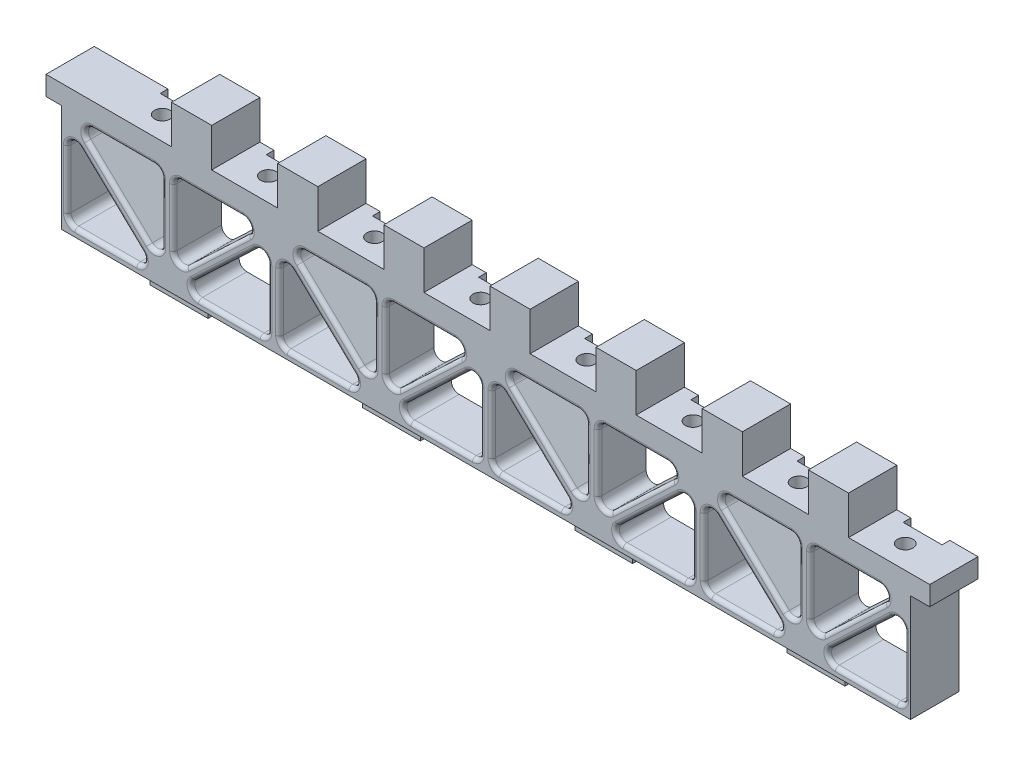
SolidWorks part; units mm, degrees
ref_plane "Front Plane" through (0, 0, 0) normal (0, 0, 1) x (1, 0, 0)
ref_plane "Top Plane" through (0, 0, 0) normal (0, 1, 0) x (1, 0, 0)
ref_plane "Right Plane" through (0, 0, 0) normal (1, 0, 0) x (0, 0, -1)
sketch "Sketch1" plane through (0, 0, 0) normal (0, 1, 0) x (1, 0, 0)
  line L1 (0, 0) -> (228.98, 0)
  line L2 (0, 0) -> (0, 12.5)
  line L3 (0, 12.5) -> (228.98, 12.5)
  line L4 (228.98, 0) -> (228.98, 12.5)
  dimension "D1" = 12.5
  dimension "D2" = 228.98
extrude "Boss-Extrude1" add sketch "Sketch1" along normal blind 5
sketch "Sketch2" plane through (0, 5, 0) normal (0, 1, 0) x (1, 0, 0)
  line L0 (228.98, 12.5) -> (0, 12.5) construction
  line L1 (19.08, 12.5) -> (29.18, 12.5)
  line L2 (19.08, 12.5) -> (19.08, 10.5)
  line L3 (19.08, 10.5) -> (29.18, 10.5)
  line L4 (29.18, 12.5) -> (29.18, 10.5)
  line L5 (0, 12.5) -> (0, 0) construction
  dimension "D1" = 19.08
  dimension "D2" = 10.1
  dimension "D3" = 2
sketch "Sketch3" plane through (0, 5, 0) normal (0, 1, 0) x (1, 0, 0)
  line L0 (0, 0) -> (228.98, 0) construction
  line L1 (19.08, 12.5) -> (19.08, 10.5) construction
  circle A0 centre (24.13, 6) radius 2
  dimension "D1" = 4
  dimension "D2" = 6
  dimension "D3" = 5.05
extrude "Cut-Extrude1" cut sketch "Sketch2" against normal blind 3.05
extrude "Cut-Extrude2" cut sketch "Sketch3" against normal blind 4
pattern_linear "LPattern1" count 8 spacing 27.5 along (1, 0, 0) of "Cut-Extrude1", "Cut-Extrude2"
sketch "Sketch4" plane through (0, 0, 0) normal (0, 0, 1) x (1, 0, 0)
  line L1 (4, 0.2046) -> (31.5, 0.2046)
  line L2 (4, 0.2046) -> (4, -27.7954)
  line L3 (4, -27.7954) -> (31.5, -27.7954)
  line L4 (31.5, 0.2046) -> (31.5, 0)
  line L5 (30, -1.2954) -> (7, -1.2954)
  line L6 (7, -1.2954) -> (30, -23.1973)
  line L7 (30, -23.1973) -> (30, -1.2954)
  line L8 (5.5, -3.8935) -> (5.5, -25.7954)
  line L9 (5.5, -25.7954) -> (28.5, -25.7954)
  line L10 (28.5, -25.7954) -> (5.5, -3.8935)
  line L11 (0, 5) -> (0, 0) construction
  line L12 (0, 0) -> (228.98, 0) construction
  line L13 (31.5, -27.7954) -> (59, -27.7954)
  line L15 (31.5, 0) -> (59, 0)
  line L16 (59, -27.7954) -> (59, 0)
  line L17 (33, -1.5) -> (33, -23.1973)
  line L18 (33, -23.1973) -> (56, -1.5)
  line L19 (56, -1.5) -> (33, -1.5)
  line L20 (34.5, -25.7954) -> (57.5, -25.7954)
  line L21 (57.5, -25.7954) -> (57.5, -4.0981)
  line L22 (57.5, -4.0981) -> (34.5, -25.7954)
  dimension "D1" = 28
  dimension "D2" = 27.5
  dimension "D3" = 1.5
  dimension "D4" = 1.5
  dimension "D5" = 2
  dimension "D6" = 1.5
  dimension "D7" = 3
  dimension "D8" = 3
  dimension "D9" = 4
  dimension "D10" = 27.5
  dimension "D11" = 1.5
  dimension "D12" = 1.5
  dimension "D13" = 1.5
  dimension "D14" = 3
  dimension "D15" = 3
  dimension "D16" = 1.5
  dimension "D17" = 1.5
  dimension "D18" = 1.5
  dimension "D19" = 1.5
extrude "Boss-Extrude2" add sketch "Sketch4" against normal blind 12.5
fillet "Fillet1" radius 2 12 edges at (57.5, -25.7954, -6.25) (57.5, -4.0981, -6.25) (30, -1.2954, -6.25) (33, -1.5, -6.25) (56, -1.5, -6.25) (5.5, -25.7954, -6.25) (5.5, -3.8935, -6.25) (7, -1.2954, -6.25) (34.5, -25.7954, -6.25) (28.5, -25.7954, -6.25) (30, -23.1973, -6.25) (33, -23.1973, -6.25)
fillet "Fillet2" radius 1 24 edges at (25.3565, -24.5381, 0) (15.4998, -25.7954, 0) (6.0858, -25.2096, 0) (5.5, -16.1776, 0) (6.7121, -6.7215, 0) (56.2922, -6.8979, 0) (57.5, -16.2649, 0) (56.9142, -25.2096, 0) (47.5173, -25.7954, 0) (37.6759, -24.5338, 0) (34.2078, -20.3975, 0) (33, -11.0306, 0) (33.5858, -2.0858, 0) (42.9827, -1.5, 0) (52.8241, -2.7616, 0) (28.7879, -20.3693, 0) (18.621, -12.3616, 0) (10.1435, -2.5527, 0) (20.0002, -1.2954, 0) (29.4142, -1.8812, 0) (16.879, -14.7292, 0) (46.1449, -14.81, 0) (44.3551, -12.4854, 0) (30, -10.9132, 0)
sketch "Sketch5" plane through (0, -27.7954, 0) normal (0, -1, 0) x (1, 0, 0)
  line L0 (4, 0) -> (59, 0) construction
  line L1 (24, -3) -> (39, -3)
  line L2 (24, -3) -> (24, -9.4)
  line L3 (24, -9.4) -> (39, -9.4)
  line L4 (39, -3) -> (39, -9.4)
  line L8 (4, 0) -> (4, -12.5) construction
  dimension "D1" = 6.4
  dimension "D2" = 3
  dimension "D3" = 15
  dimension "D4" = 20
extrude "Boss-Extrude3" add sketch "Sketch5" along normal blind 4
pattern_linear "LPattern2" count 4 spacing 55 along (1, 0, 0) of "Boss-Extrude2", "Fillet1", "Fillet2", "Boss-Extrude3"
sketch "Sketch6" plane through (0, 5, 0) normal (0, 1, 0) x (1, 0, 0)
  line L0 (46.58, 12.5) -> (29.18, 12.5) construction
  line L1 (32.53, 12.5) -> (42.93, 12.5)
  line L2 (32.53, 12.5) -> (32.53, 0)
  line L3 (32.53, 0) -> (42.93, 0)
  line L4 (42.93, 12.5) -> (42.93, 0)
  line L5 (0, 0) -> (228.98, 0) construction
  line L6 (29.18, 10.5) -> (29.18, 12.5) construction
  dimension "D1" = 3.35
  dimension "D2" = 10.4
extrude "Boss-Extrude4" add sketch "Sketch6" along normal blind 10
pattern_linear "LPattern3" count 7 spacing 27.5 along (1, 0, 0) of "Boss-Extrude4"
